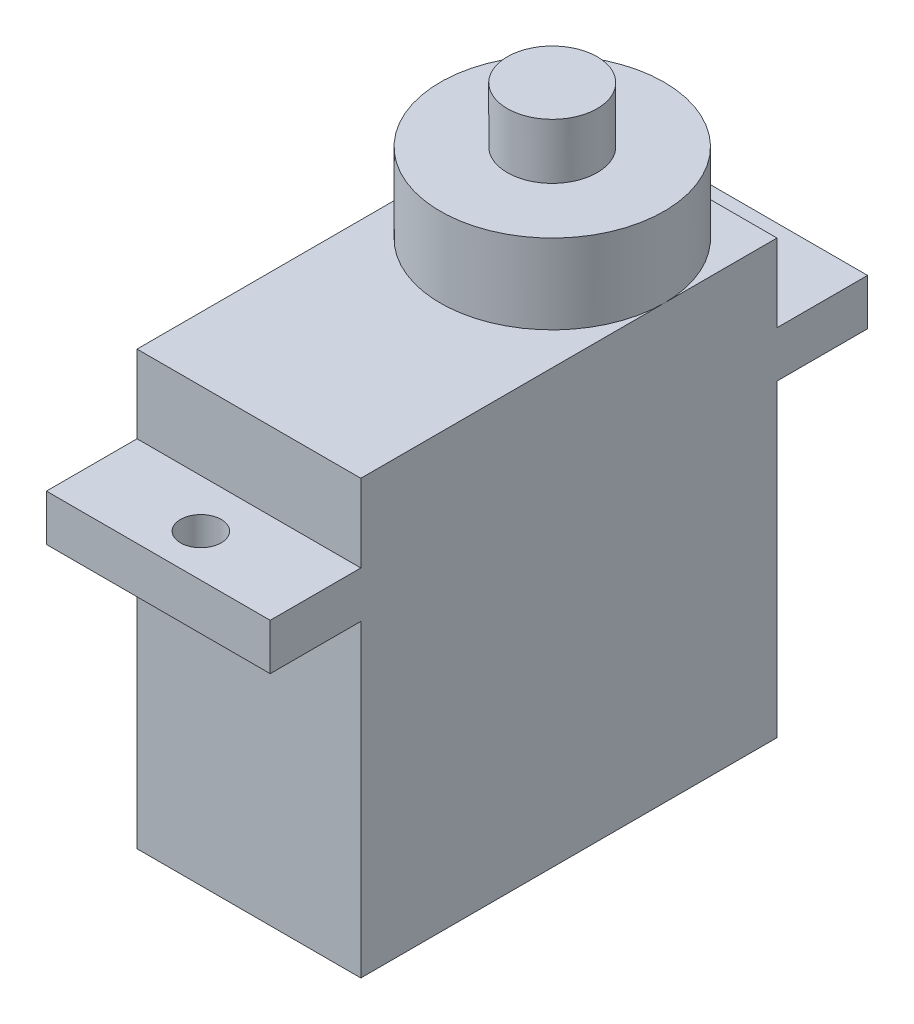
SolidWorks part; units mm, degrees
material "ABS"
ref_plane "Front Plane" through (0, 0, 0) normal (0, 0, 1) x (1, 0, 0)
ref_plane "Top Plane" through (0, 0, 0) normal (0, 1, 0) x (1, 0, 0)
ref_plane "Right Plane" through (0, 0, 0) normal (1, 0, 0) x (0, 0, -1)
sketch "Sketch1" plane through (0, 0, 0) normal (1, 0, 0) x (0, 0, -1)
  line L0 (0, 0) -> (22.5, 0)
  line L1 (22.5, 0) -> (22.5, 16.7)
  line L2 (22.5, 16.7) -> (27.4, 16.7)
  line L3 (27.4, 16.7) -> (27.4, 19.2)
  line L4 (27.4, 19.2) -> (22.5, 19.2)
  line L5 (22.5, 19.2) -> (22.5, 23.4)
  line L6 (22.5, 23.4) -> (0, 23.4)
  line L7 (0, 23.4) -> (0, 19.2)
  line L8 (0, 19.2) -> (-4.9, 19.2)
  line L9 (-4.9, 19.2) -> (-4.9, 16.7)
  line L10 (-4.9, 16.7) -> (0, 16.7)
  line L11 (0, 16.7) -> (0, 0)
  dimension "D1" = 22.5
  dimension "D2" = 16.7
  dimension "D3" = 23.4
  dimension "D4" = 19.2
  dimension "D5" = 32.3
extrude "Boss-Extrude1" add sketch "Sketch1" along normal blind 12.1
sketch "Sketch2" plane through (0, 19.2, 0) normal (0, 1, 0) x (1, 0, 0)
  line L0 (6.05, 25.1) -> (6.05, -2.6) construction
  line L1 (0, 11.25) -> (12.1, 11.25) construction
  line L2 (0, 22.5) -> (0, 0) construction
  line L3 (12.1, 22.5) -> (12.1, 0) construction
  circle A0 centre (6.05, -2.6) radius 1.1
  circle A1 centre (6.05, 25.1) radius 1.1
  point P10 (3.3237, 17.6004)
  point P11 (6.05, 11.25)
  point P12 (3.6927, 17.3698)
  dimension "D2" = 2.2
  dimension "D1" = 27.7
extrude "Cut-Extrude1" cut sketch "Sketch2" against normal through all
ref_plane "Plane1" through (0, 27.7, 0) normal (0, -1, 0) x (-1, 0, 0)
ref_plane "Plane2" through (0, 30.7, 0) normal (0, -1, 0) x (-1, 0, 0)
sketch "Sketch3" plane through (0, 23.4, 0) normal (0, 1, 0) x (1, 0, 0)
  line L0 (6.05, 22.5) -> (6.05, 0) construction
  line L1 (12.1, 22.5) -> (0, 22.5) construction
  line L2 (12.1, 0) -> (0, 0) construction
  line L3 (12.1, 22.5) -> (12.1, 0) construction
  circle A0 centre (6.05, 16.4) radius 6.05
  circle A1 centre (6.05, 25.1) radius 1.1 construction
  point P8 (0, 0)
  dimension "D1" = 8.7
extrude "Boss-Extrude3" add sketch "Sketch3" along normal up to surface (4.3 mm away) up to plane "Plane1"
sketch "Sketch4" plane through (0, 27.7, 0) normal (0, 1, 0) x (1, 0, 0)
  circle A0 centre (6.05, 16.4) radius 2.43
  arc A1 (0, 16.4) -> (12.1, 16.4) centre (6.05, 16.4) ccw construction
  dimension "D1" = 4.86
extrude "Boss-Extrude4" add sketch "Sketch4" along normal up to surface (3 mm away) up to plane "Plane2"
